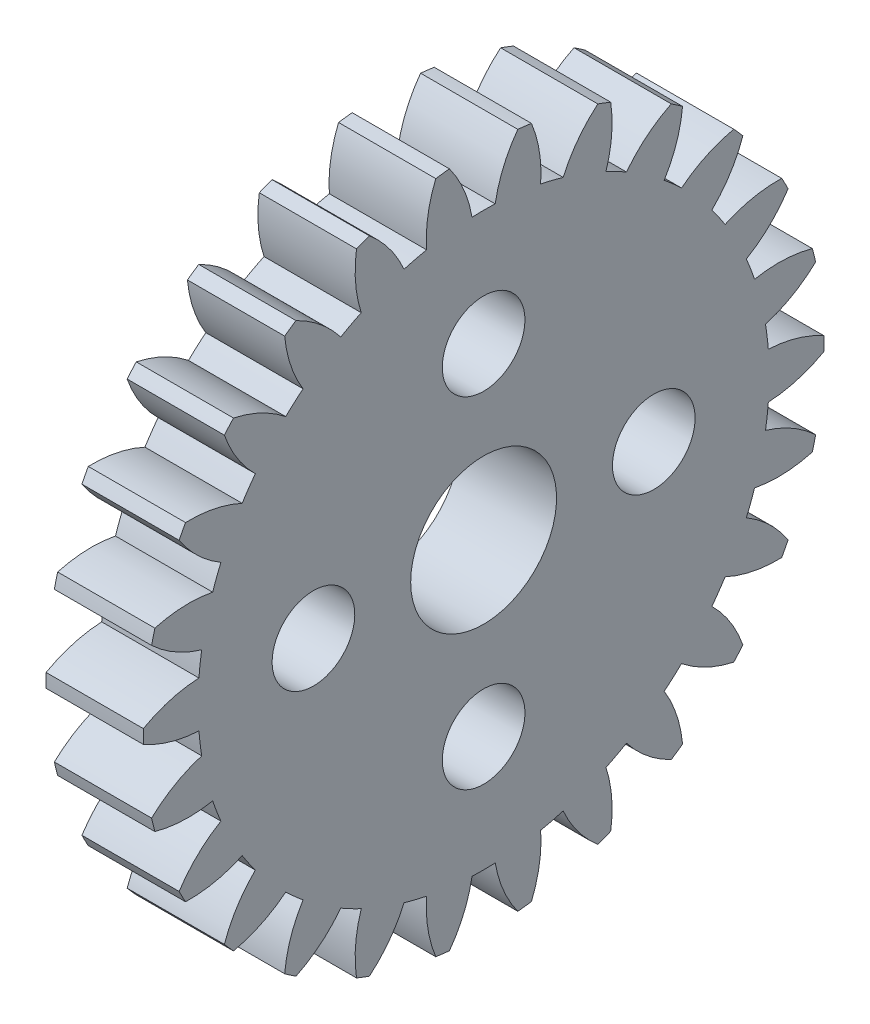
SolidWorks part; units mm, degrees
ref_plane "Plane1" through (0, 0, 0) normal (0, 0, 1) x (1, 0, 0)
ref_plane "Plane2" through (0, 0, 0) normal (0, 1, 0) x (1, 0, 0)
ref_plane "Plane3" through (0, 0, 0) normal (1, 0, 0) x (0, 0, -1)
sketch "HoldingSke" plane through (0, 0, 0) normal (0, 1, 0) x (1, 0, 0)
  line L0 (0, 0) -> (0.8988, -0.4384)
  line L1 (-15, 0) -> (100, 0) construction
  line L2 (0, 0) -> (-2.1039, 2.3779)
  line L3 (0, 0) -> (-11.863, 4.5341)
  line L4 (0, 0) -> (7.762, 3.7858)
  line L5 (0, 0) -> (-46.8476, -17.4728)
  line L6 (0, 0) -> (-3.3159, -2.2372)
  line L7 (-2.1039, 2.3779) -> (8.6586, 51.2059)
  line L8 (-76.2, 54.61) -> (-75.2, 54.61)
  line L9 (-71.009, 38.7566) -> (-53.1078, 45.2721)
  line L10 (-76.2, 71.12) -> (104.1128, 71.12)
  line L11 (0, 0) -> (-4, 0)
  line L12 (-76.2, 101.6) -> (-76.162, 101.6)
  line L13 (24.9733, 27.94) -> (52.9518, 28.4284)
  line L14 (24.9733, 27.94) -> (24.9743, 27.94)
  line L15 (24.9733, 27.94) -> (100.4006, 29.5858)
  line L16 (-63.627, -1) -> (-12.827, -1)
  circle A0 centre (0, 0) radius 3
  circle A1 centre (0, 0) radius 11.749
  circle A2 centre (0, 0) radius 37.5
  circle A3 centre (0, 0) radius 3
  dimension "MHD" = 23.498
  dimension "Hub_dia" = 75
  dimension "Bore" = 6
  dimension "MBD" = 6
  dimension "Num_teeth" = 26
  dimension "Pitch" = 1
  dimension "Overall_len" = 50
  dimension "Show_teeth" = 26
  dimension "Thickness" = 4
  dimension "OAL" = 50.0001
  dimension "T_dim" = 1
  dimension "Ap" = 20
  dimension "H" = 19.05
  dimension "Pitch_radius" = 180.3128
  dimension "Width" = 4
  dimension "Backlash" = 0.038
  dimension "Addendum_fac" = 1
  dimension "Dedendum_fac" = 1.25
  dimension "Clearance_fac" = 0.25
  dimension "Dedendum_add" = 0.001
  dimension "Module" = 1
sketch "BasProSke" plane through (0, 0, 0) normal (0, 1, 0) x (1, 0, 0)
  line L0 (-10, 0) -> (60, 0) construction
  line L1 (0, 0) -> (0, 14)
  line L2 (0, 0) -> (4, 0)
  line L3 (4, 0) -> (4, 14)
  line L4 (4, 14) -> (0, 14)
  dimension "Thickness" = 4
  dimension "Diameter" = 28
revolve "Base-Revolve" add sketch "BasProSke" angle 360 about L0
sketch "TooCutSke" plane through (0, 0, 0) normal (1, 0, 0) x (0, 0, -1)
  line L1 (0, 0) -> (0, 107) construction
  line L2 (0, 0) -> (-0.8514, 12.9721) construction
  line L3 (0, 0) -> (-3.1292, 25.771) construction
  line L4 (-0.8514, 12.9721) -> (-1.5646, 12.8855) construction
  arc A0 (0.477, 11.7393) -> (-0.477, 11.7393) centre (0, 0) ccw
  arc A1 (1.4241, 13.9529) -> (-1.4241, 13.9529) centre (0, 0) ccw
  circle A2 centre (0, 0) radius 13 construction
  circle A3 centre (0, 0) radius 12.216 construction
  arc A4 (-0.477, 11.7393) -> (-1.4241, 13.9529) centre (-5.6014, 10.8561) ccw
  arc A5 (1.4241, 13.9529) -> (0.477, 11.7393) centre (5.6014, 10.8561) ccw
  dimension "Root_dia" = 23.498
  dimension "Overcut_dia" = 28.0508
  dimension "Pitch_dia" = 26
  dimension "Base_dia" = 24.432
  dimension "Flank_rad" = 5.2
  dimension "Half_ang" = 6.923
  dimension "Half_CT" = 0.7184
extrude "ToothCut" cut sketch "TooCutSke" along normal through all
fillet "Breaks" [suppressed] radius 0.02
fillet "RootFillets" [suppressed] radius 0.251
pattern_circular "TeethCuts" count 26 every 13.846 about axis through (-10, 0, 0) along (1, 0, 0) of "ToothCut", "RootFillets", "Breaks"
sketch "HubNeaOneSke" plane through (0, 0, 0) normal (-1, 0, 0) x (0, 0, 1)
  circle A0 centre (0, 0) radius 11.749
  dimension "Diameter" = 23.498
extrude "HubNearOne" [suppressed] add sketch "HubNeaOneSke" along normal blind 46.0001
sketch "HubNeaBotSke" plane through (0, 0, 0) normal (-1, 0, 0) x (0, 0, 1)
  circle A0 centre (0, 0) radius 11.749
  dimension "Diameter" = 23.498
extrude "HubNearBoth" [suppressed] add sketch "HubNeaBotSke" along normal blind 23
ref_plane "FarPln" through (4, 0, 0) normal (1, 0, 0) x (0, 0, -1)
sketch "HubFarSke" plane through (4, 0, 0) normal (1, 0, 0) x (0, 0, -1)
  circle A0 centre (0, 0) radius 11.749
  dimension "Diameter" = 23.498
extrude "HubFar" [suppressed] add sketch "HubFarSke" along normal blind 23
sketch "BorSke" plane through (0, 0, 0) normal (1, 0, 0) x (0, 0, -1)
  circle A0 centre (0, 0) radius 3
  dimension "Diameter" = 6
extrude "Bore" cut sketch "BorSke" along normal mid plane 100.0001
sketch "KeySke" plane through (0, 0, 0) normal (1, 0, 0) x (0, 0, -1)
  line L0 (-1, 0) -> (-1, 4)
  line L1 (-1, 4) -> (1, 4)
  line L2 (1, 4) -> (1, 0)
  line L3 (0, 0) -> (0, 34) construction
  line L4 (-1, 0) -> (1, 0)
  dimension "Offset" = 4
  dimension "Width" = 2
extrude "Keyway" [suppressed] cut sketch "KeySke" along normal mid plane 100.0001
pattern_circular "Keyway2" [suppressed] count 2 every 90 about axis through (-10, 0, 0) along (1, 0, 0)
hole_wizard "M3 餘隙孔1" positions "Sketch1" profile "Sketch2" hole size "M3" standard "Ansi Metric" end condition through all
sketch "Sketch1" plane through (4, 0, 0) normal (1, 0, 0) x (0, 0, -1)
  line L0 (0, 0) -> (0, 7) construction
  point P2 (0, 7)
  dimension "D1" = 7
sketch "Sketch2" plane through (4, 7, 0) normal (0, 1, 0) x (0, 0, -1)
  line L0 (0, 0) -> (0, 4)
  line L1 (0, 4) -> (1.7, 4)
  line L2 (1.7, 4) -> (1.7, 0)
  line L5 (1.7, 0) -> (0, 0)
  line L11 (0, -6.35) -> (0, 107.95) construction
  dimension "Thru Hole Dia." = 3.4
  dimension "Thru Hole Depth" = 4
pattern_circular "CirPattern1" count 4 over 360 about axis through (0, 0, 0) along (1, 0, 0) of "M3 餘隙孔1"
equation "' \"Module@HoldingSke\" = 6.35"
equation "' \"Num_teeth@HoldingSke\" = 12"
equation "' \"Ap@HoldingSke\" =  20"
equation "' \"Ap@HoldingSke\" = 20"
equation "' \"Width@HoldingSke\" = 0.5 * 25.4"
equation "' \"Hub_dia@HoldingSke\"= 1 * 25.4"
equation "' \"Hub_dia@HoldingSke\" = 1 * 25.4"
equation "' \"Overall_len@HoldingSke\" = 1.0 * 25.4"
equation "' \"Bore@HoldingSke\" = 0.75 * 25.4"
equation "' \"T_dim@HoldingSke\" = 0.1 * 25.4"
equation "' \"Width@KeySke\" = 0.25 * 25.4"
equation "' \"Show_teeth@HoldingSke\" = 13"
equation "' \"Backlash@HoldingSke\" = 0.009 * 25.4"
equation "' \"Addendum_fac@HoldingSke\" = 1.0"
equation "' \"Dedendum_fac@HoldingSke\" = 1.25"
equation "' \"Dedendum_add@HoldingSke\" = 0.00005 * 25.4"
equation "' \"Clearance_fac@HoldingSke\" = 0.25"
equation "\"Pitch@HoldingSke\" = 1 / \"Module@HoldingSke\""
equation "\"Overcut_dia@TooCutSke\" = (\"Num_teeth@HoldingSke\" + 2 * \"Addendum_fac@HoldingSke\") / \"Pitch@HoldingSke\" + 0.002 * 25.4"
equation "\"Pitch_dia@TooCutSke\" = \"Num_teeth@HoldingSke\" / \"Pitch@HoldingSke\""
equation "\"Base_dia@TooCutSke\" = \"Num_teeth@HoldingSke\" / \"Pitch@HoldingSke\" * cos((\"Ap@HoldingSke\"  * 3.14159265 / 180))"
equation "\"Root_dia@TooCutSke\" = (\"Num_teeth@HoldingSke\" + 2) / \"Pitch@HoldingSke\" - 2 * (\"Addendum_fac@HoldingSke\" + \"Dedendum_fac@HoldingSke\") / \"Pitch@HoldingSke\" - \"Dedendum_add@HoldingSke\" * 2"
equation "\"Half_ang@TooCutSke\" = 180 / \"Num_teeth@HoldingSke\""
equation "\"Half_CT@TooCutSke\" = \"Num_teeth@HoldingSke\" / \"Pitch@HoldingSke\" * sin((3.14159265 / 2 / \"Num_teeth@HoldingSke\")) / 2 - 7 * \"Backlash@HoldingSke\" / 4"
equation "\"Flank_rad@TooCutSke\" = \"Num_teeth@HoldingSke\" / \"Pitch@HoldingSke\" / 5"
equation "\"Radius@RootFillets\" = \"Clearance_fac@HoldingSke\" / \"Pitch@HoldingSke\" + \"Dedendum_add@HoldingSke\""
equation "\"Break_rad@Breaks\" = 0.02 / \"Pitch@HoldingSke\""
equation "\"Thickness@HoldingSke\" = \"Width@HoldingSke\""
equation "\"OAL@HoldingSke\" = \"Thickness@HoldingSke\""
equation "\"MHD@HoldingSke\" = (\"Num_teeth@HoldingSke\" + 2) / \"Pitch@HoldingSke\" - 2 * (\"Addendum_fac@HoldingSke\" + \"Dedendum_fac@HoldingSke\")  / \"Pitch@HoldingSke\" - \"Dedendum_add@HoldingSke\" * 2"
equation "\"MBD@HoldingSke\" = (\"Num_teeth@HoldingSke\" + 2) / \"Pitch@HoldingSke\" - 2 * (\"Addendum_fac@HoldingSke\" + \"Dedendum_fac@HoldingSke\")  / \"Pitch@HoldingSke\" - \"Dedendum_add@HoldingSke\" * 2 - 0.002 * 25.4"
equation "\"MHD@HoldingSke\" = ((sgn( \"MHD@HoldingSke\" - \"Hub_dia@HoldingSke\" )-1)*( \"MHD@HoldingSke\" - \"Hub_dia@HoldingSke\" ))/-2+ \"Hub_dia@HoldingSke\""
equation "\"MBD@HoldingSke\" = ((sgn( \"MBD@HoldingSke\" - \"Bore@HoldingSke\" )-1)*( \"MBD@HoldingSke\" - \"Bore@HoldingSke\" ))/-2+ \"Bore@HoldingSke\""
equation "\"OAL@HoldingSke\" = ((sgn( \"OAL@HoldingSke\" - \"Overall_len@HoldingSke\" )+1)*( \"OAL@HoldingSke\" - \"Overall_len@HoldingSke\" ))/2 + \"Overall_len@HoldingSke\" + 0.000002 * 25.4"
equation "\"Num_teeth@TeethCuts\" = int( \"Show_teeth@HoldingSke\" ) + 1"
equation "\"Num_teeth@TeethCuts\" = ((sgn( \"Num_teeth@TeethCuts\" - \"Num_teeth@HoldingSke\" )-1)*( \"Num_teeth@TeethCuts\" - \"Num_teeth@HoldingSke\" ))/-2+ \"Num_teeth@HoldingSke\""
equation "\"Num_teeth@TeethCuts\" = ((sgn( \"Num_teeth@TeethCuts\" - 2.0)+1)*( \"Num_teeth@TeethCuts\" - 2.0))/2 +2.0"
equation "\"Angle@TeethCuts\" = 360.0 / \"Num_teeth@HoldingSke\""
equation "\"Diameter@BasProSke\" = (\"Num_teeth@HoldingSke\" + 2 * \"Addendum_fac@HoldingSke\") / \"Pitch@HoldingSke\""
equation "\"Thickness@BasProSke\"  = \"Thickness@HoldingSke\""
equation "' \"Fillet_rad@BasProSke\" =  \"Thickness@HoldingSke\" * 0.05"
equation "' \"Fillet_rad@BasProSke\" = \"Thickness@HoldingSke\" * 0.05"
equation "\"MHD@HoldingSke\" = ((sgn( \"MHD@HoldingSke\" - \"Root_dia@TooCutSke\" )-1)*( \"MHD@HoldingSke\" - \"Root_dia@TooCutSke\" ))/-2+ \"Root_dia@TooCutSke\""
equation "\"Diameter@HubNeaOneSke\" = \"MHD@HoldingSke\""
equation "\"Length@HubNearOne\" = \"OAL@HoldingSke\" - \"Thickness@BasProSke\""
equation "\"Diameter@HubNeaBotSke\" = \"MHD@HoldingSke\""
equation "\"Length@HubNearBoth\" = ( \"OAL@HoldingSke\" - \"Thickness@BasProSke\" ) / 2.0"
equation "\"Thickness@FarPln\" = \"Thickness@BasProSke\""
equation "\"Diameter@HubFarSke\" = \"MHD@HoldingSke\""
equation "\"Length@HubFar\" = ( \"OAL@HoldingSke\" - \"Thickness@BasProSke\" ) / 2.0"
equation "\"Diameter@BorSke\" = \"MBD@HoldingSke\""
equation "\"D1@Bore\" = \"OAL@HoldingSke\" * 2.0"
equation "\"D1@Keyway\" = \"OAL@HoldingSke\" * 2.0"
equation "\"Offset@KeySke\" = \"T_dim@HoldingSke\" + \"MBD@HoldingSke\" / 2.0"
